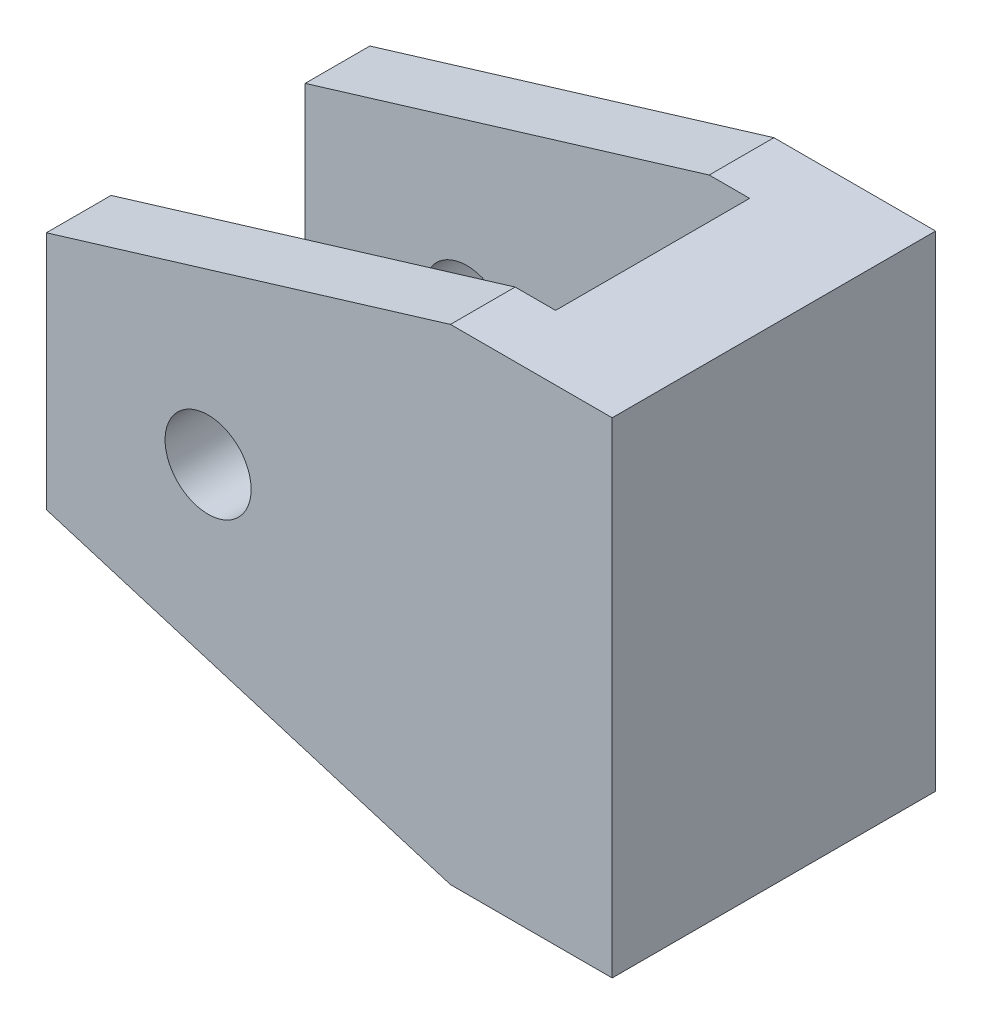
SolidWorks part; units mm, degrees
ref_plane "Front" through (0, 0, 0) normal (0, 0, 1) x (1, 0, 0)
ref_plane "Top" through (0, 0, 0) normal (0, 1, 0) x (1, 0, 0)
ref_plane "Right" through (0, 0, 0) normal (1, 0, 0) x (0, 0, -1)
sketch "Sketch1" plane through (0, 0, 0) normal (0, 0, 1) x (1, 0, 0)
  line L0 (556.9941, -1558.6566) -> (556.9941, -1577.4907)
  line L1 (601.4273, -1549.0237) -> (601.4273, -1587.1237)
  line L4 (601.4273, -1549.0237) -> (588.7273, -1549.0237)
  line L5 (588.7273, -1549.0237) -> (556.9941, -1558.6566)
  line L6 (556.9941, -1577.4907) -> (588.7273, -1587.1237)
  line L7 (588.7273, -1587.1237) -> (601.4273, -1587.1237)
  line L8 (588.7273, -1587.1237) -> (601.4273, -1587.1237) construction
  line L9 (588.7273, -1549.0237) -> (601.4273, -1549.0237) construction
  circle A0 centre (569.6941, -1568.0737) radius 12.7 construction
  point P6 (556.9941, -1568.0737)
  dimension "D1" = 25.4
extrude "Boss-Extrude1" add sketch "Sketch1" along normal up to surface (12.7 mm away) and the other way up to surface (12.7 mm away)
sketch "Sketch2" plane through (0, -1587.1237, 0) normal (0, -1, 0) x (1, 0, 0)
  line L1 (591.9023, 7.62) -> (556.9941, 7.62)
  line L2 (591.9023, 7.62) -> (591.9023, -7.62)
  line L3 (591.9023, -7.62) -> (556.9941, -7.62)
  line L4 (556.9941, 7.62) -> (556.9941, -7.62)
  line L5 (556.9941, 12.7) -> (556.9941, -12.7) construction
  line L6 (601.4273, -12.7) -> (601.4273, 12.7) construction
  line L7 (601.4273, 12.7) -> (601.4273, -12.7) construction
  point P11 (601.4273, 0)
  point P12 (591.9023, 0)
  dimension "D1" = 9.525
  dimension "D2" = 15.24
extrude "Cut-Extrude1" cut sketch "Sketch2" against normal up to surface (38.1 mm away) up to face at (595.0773, -1549.0237, 0)
hole_wizard "1/4 Clearance Hole1" positions "Sketch4" profile "Sketch5" hole size "1/4" standard "ANSI Inch"
sketch "Sketch4" plane through (0, 0, 12.7) normal (0, 0, 1) x (1, 0, 0)
  point P0 (569.6941, -1568.0737)
sketch "Sketch5" plane through (569.6941, -1568.0737, 12.7) normal (1, 0, 0) x (0, -1, 0)
  line L0 (0, 0) -> (0, 27.4298)
  line L1 (0, 27.4298) -> (3.3782, 25.4)
  line L2 (3.3782, 25.4) -> (3.3782, 0)
  line L5 (3.3782, 0) -> (0, 0)
  line L10 (0, 27.4298) -> (-3.3782, 25.4) construction
  line L11 (0, -6.35) -> (0, 107.95) construction
  dimension "Hole Dia." = 6.7564
  dimension "Hole Depth" = 25.4
  dimension "Drill Angle" = 118
